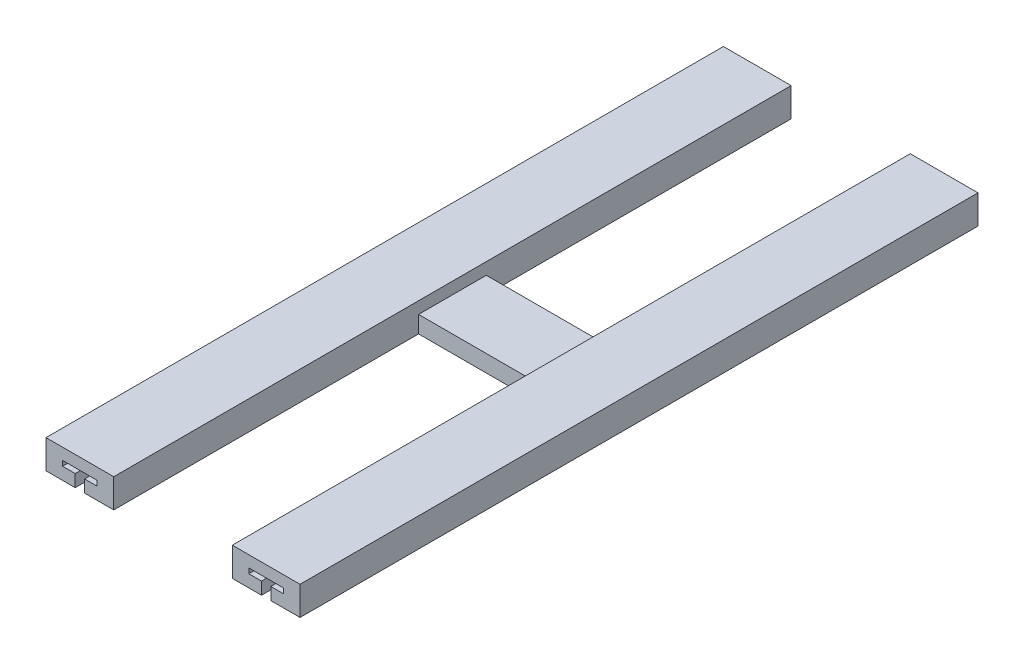
SolidWorks part; units mm, degrees
ref_plane "Front Plane" through (0, 0, 0) normal (0, 0, 1) x (1, 0, 0)
ref_plane "Top Plane" through (0, 0, 0) normal (0, 1, 0) x (1, 0, 0)
ref_plane "Right Plane" through (0, 0, 0) normal (1, 0, 0) x (0, 0, -1)
sketch "Sketch1" plane through (0, 0, 0) normal (0, 1, 0) x (1, 0, 0)
  line L0 (40, 449.6681) -> (40, 269.6681)
  line L1 (0, 449.6681) -> (40, 449.6681)
  line L2 (0, 49.6681) -> (0, 449.6681)
  line L3 (0, 49.6681) -> (40, 49.6681)
  line L4 (150, 10) -> (150, 450)
  line L5 (110, 450) -> (110, 269.6681)
  line L6 (110, 450) -> (150, 450)
  line L7 (110, 10) -> (150, 10)
  line L8 (40, 269.6681) -> (110, 269.6681)
  line L9 (40, 229.6681) -> (110, 229.6681)
  line L10 (0, 249.6681) -> (279.0452, 249.6681) construction
  line L11 (40, 229.6681) -> (40, 49.6681)
  line L12 (110, 229.6681) -> (110, 10)
  dimension "D1" = 400
  dimension "D2" = 440
  dimension "D3" = 40
  dimension "D4" = 40
  dimension "D5" = 40
extrude "Boss-Extrude1" add sketch "Sketch1" along normal blind 17
sketch "Sketch2" plane through (0, 17, 0) normal (0, 1, 0) x (1, 0, 0)
  line L1 (40, 269.6681) -> (110, 269.6681)
  line L2 (40, 269.6681) -> (40, 229.6681)
  line L3 (40, 229.6681) -> (110, 229.6681)
  line L4 (110, 269.6681) -> (110, 229.6681)
extrude "Cut-Extrude1" cut sketch "Sketch2" against normal blind 7
sketch "Sketch3" plane through (0, 0, -49.6681) normal (0, 0, 1) x (1, 0, 0)
  line L0 (20, 0) -> (20, 20.682) construction
  line L1 (0, 0) -> (40, 0) construction
  line L2 (17.25, 0) -> (17.25, 7.25)
  line L3 (17.25, 7.25) -> (9.75, 7.25)
  line L4 (9.75, 7.25) -> (9.75, 10.25)
  line L5 (9.75, 10.25) -> (30.25, 10.25)
  line L6 (30.25, 10.25) -> (30.25, 7.25)
  line L7 (30.25, 7.25) -> (22.75, 7.25)
  line L8 (22.75, 7.25) -> (22.75, 0)
  line L9 (22.75, 0) -> (17.25, 0)
  line L10 (9.75, 8.75) -> (36.0403, 8.75) construction
  dimension "D1" = 20.5
  dimension "D2" = 3
  dimension "D3" = 5.5
  dimension "D4" = 10.25
extrude "Cut-Extrude2" cut sketch "Sketch3" against normal through all
ref_plane "Plane1" through (75, 0, 0) normal (1, 0, 0) x (0, 0, -1)
mirror "Mirror1" about plane through (75, 0, 0) normal (1, 0, 0) of "Cut-Extrude2"
sketch "Sketch4" plane through (0, 17, 0) normal (0, 1, 0) x (1, 0, 0)
  line L1 (0, 49.6681) -> (150, 49.6681)
  line L2 (0, 49.6681) -> (0, 10)
  line L3 (0, 10) -> (150, 10)
  line L4 (150, 49.6681) -> (150, 10)
extrude "Cut-Extrude3" cut sketch "Sketch4" against normal through all both and the other way through all
